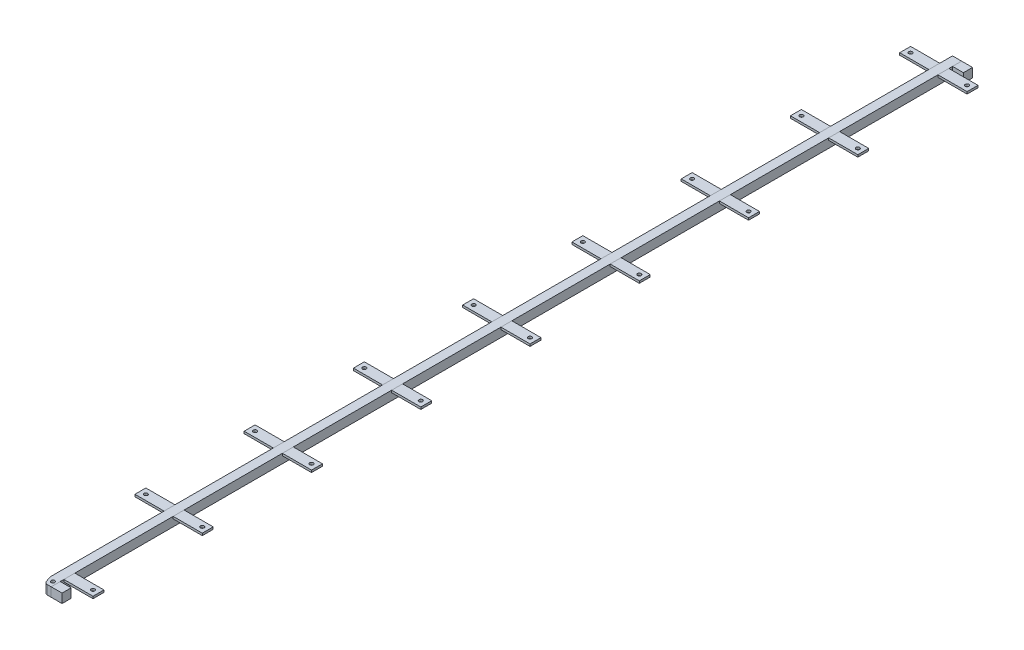
SolidWorks part; units mm, degrees
material "普通碳钢"
ref_plane "前视基准面" through (0, 0, 0) normal (0, 0, 1) x (1, 0, 0)
ref_plane "上视基准面" through (0, 0, 0) normal (0, 1, 0) x (1, 0, 0)
ref_plane "右视基准面" through (0, 0, 0) normal (1, 0, 0) x (0, 0, -1)
sketch "草图1" plane through (0, 0, 0) normal (0, 1, 0) x (1, 0, 0)
  line L0 (0, 0) -> (0, 2500)
  line L1 (0, 2500) -> (25, 2500)
  line L2 (25, 2500) -> (25, 0)
  line L3 (25, 0) -> (0, 0)
  dimension "D1" = 2500
  dimension "D2" = 25
extrude "凸台-拉伸1" add sketch "草图1" along normal blind 25
sketch "草图2" plane through (0, 0, 0) normal (0, 1, 0) x (1, 0, 0)
  line L1 (25, 0) -> (55, 0)
  line L2 (25, 0) -> (25, 25)
  line L3 (25, 25) -> (55, 25)
  line L4 (55, 0) -> (55, 25)
  dimension "D1" = 30
  dimension "D2" = 25
extrude "凸台-拉伸2" add sketch "草图2" along normal blind 25 separate body
chamfer "倒角1" distance 22 distance2 8 1 edges at (0, 12.5, 0)
fillet "圆角2" radius 10 2 edges at (0, 12.5, -22) (8, 12.5, 0)
sketch "草图3" plane through (0, 0, -2500) normal (0, 0, -1) x (-1, 0, 0)
  line L1 (-25, 25) -> (-55, 25)
  line L2 (-25, 25) -> (-25, 0)
  line L3 (-25, 0) -> (-55, 0)
  line L4 (-55, 25) -> (-55, 0)
  dimension "D1" = 30
  dimension "D2" = 25
extrude "凸台-拉伸3" add sketch "草图3" against normal blind 25 separate body
sketch "草图4" plane through (0, 25, 0) normal (0, 1, 0) x (1, 0, 0)
  line L0 (0, 2500) -> (0, 23.7617) construction
  line L5 (0, 2465) -> (-80, 2465)
  line L6 (0, 2465) -> (0, 2435)
  line L7 (0, 2435) -> (-80, 2435)
  line L8 (-80, 2465) -> (-80, 2435)
  line L9 (25, 0) -> (25, 2500) construction
  line L10 (25, 2465) -> (105, 2465)
  line L11 (25, 2465) -> (25, 2435)
  line L12 (25, 2435) -> (105, 2435)
  line L13 (105, 2465) -> (105, 2435)
  line L14 (25, 2500) -> (55, 2500) construction
  line L19 (25, 2500) -> (0, 2500) construction
  line L20 (105, 2450) -> (-20, 2450) construction
  circle A0 centre (90, 2450) radius 5
  circle A1 centre (-65, 2450) radius 5
  point P22 (25, 2450)
  dimension "D7" = 65
  dimension "D9" = 10
  dimension "D1" = 30
  dimension "D2" = 30
  dimension "D3" = 80
  dimension "D4" = 80
  dimension "D5" = 35
  dimension "D6" = 35
  dimension "D8" = 65
extrude "凸台-拉伸4" add sketch "草图4" against normal blind 6 separate body
pattern_linear "阵列(线性)1" count 9 spacing 300 along (0, 0, 1) of "凸台-拉伸4"
sketch "草图5" plane through (0, 0, 0) normal (0, -1, 0) x (1, 0, 0)
  line L0 (25, 0) -> (25, -2500) construction
  line L1 (15.0043, 0) -> (25, 0) construction
  circle A0 centre (15, -15) radius 5
  dimension "D1" = 10
  dimension "D3" = 10
  dimension "D2" = 15
extrude "切除-拉伸3" cut sketch "草图5" against normal up to next (25 mm away)
sketch "草图6" plane through (0, 19, 0) normal (0, -1, 0) x (-1, 0, 0)
  line L0 (80, 65) -> (80, 35) construction
  line L1 (80, 35) -> (0, 35)
  line L2 (80, 35) -> (80, 65)
  line L3 (80, 65) -> (0, 65)
  line L4 (0, 35) -> (0, 65)
  line L5 (80, 35) -> (0, 35) construction
  line L6 (0, 65) -> (80, 65) construction
extrude "切除-拉伸4" cut sketch "草图6" against normal blind 10
